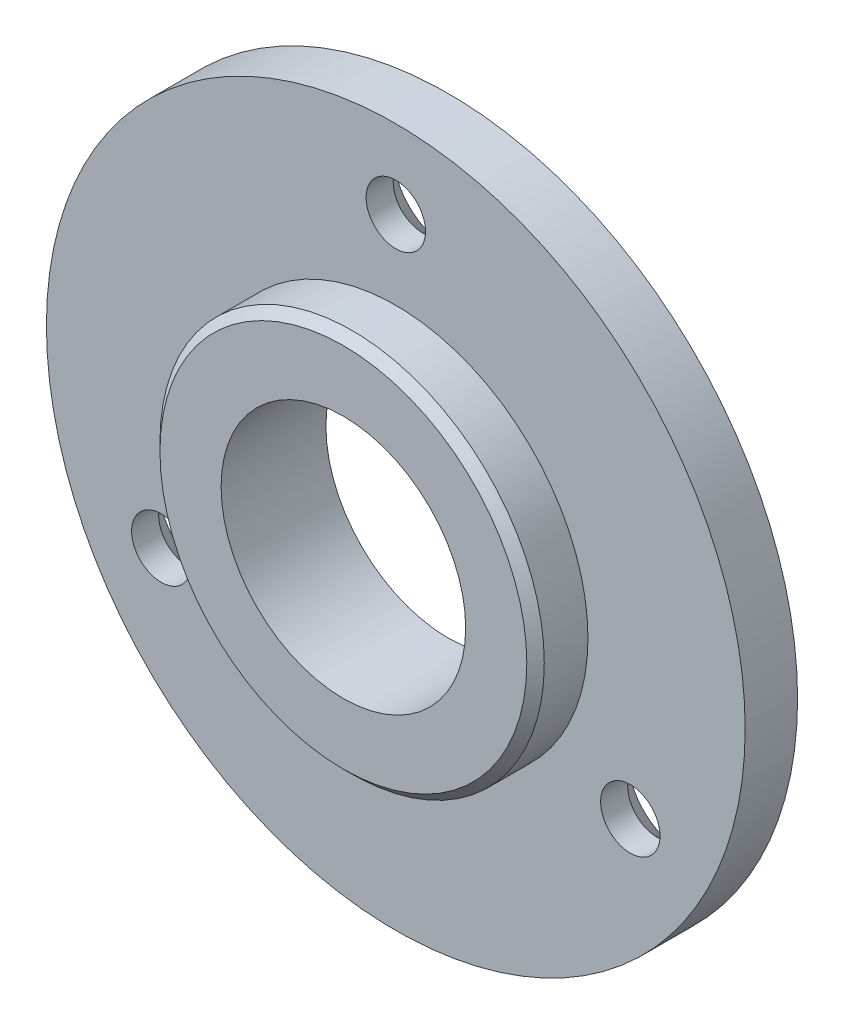
SolidWorks part; units mm, degrees
material "3.1325 (EN-AW 2017A)"
ref_plane "Plan de face" through (0, 0, 0) normal (0, 0, 1) x (1, 0, 0)
ref_plane "Plan de dessus" through (0, 0, 0) normal (0, 1, 0) x (1, 0, 0)
ref_plane "Plan de droite" through (0, 0, 0) normal (1, 0, 0) x (0, 0, -1)
sketch "Esquisse1" plane through (0, 0, 0) normal (0, 0, 1) x (1, 0, 0)
  circle A0 centre (0, 0) radius 20
extrude "Boss.-Extru.1" add sketch "Esquisse1" along normal blind 3
sketch "Esquisse2" plane through (0, 0, 3) normal (0, 0, 1) x (1, 0, 0)
  circle A0 centre (0, 0) radius 11
extrude "Boss.-Extru.2" add sketch "Esquisse2" along normal blind 3
chamfer "Chanfrein1" distance 0.5 angle 45 1 edges at (11, 0, 6)
sketch "Esquisse3" plane through (0, 0, 0) normal (0, 0, -1) x (-1, 0, 0)
  circle A0 centre (0, 0) radius 7
extrude "Enlèv. mat.-Extru.1" cut sketch "Esquisse3" against normal through all
hole_wizard "Fraisage pour vis à tête fraisée M32" positions "Esquisse12" profile "Esquisse11" countersink size "M3" standard "ISO" end condition through all
sketch "Esquisse12" plane through (0, 0, 0) normal (0, 0, -1) x (-1, 0, 0)
  point P0 (0, 15.5)
  dimension "D1" = 0
  dimension "D2" = 15.5
sketch "Esquisse11" plane through (0, 15.5, 0) normal (1, 0, 0) x (0, 1, 0)
  line L0 (0, 0) -> (0, 6)
  line L1 (0, 6) -> (1.7, 6)
  line L2 (1.7, 6) -> (1.7, 1.45)
  line L3 (1.7, 1.45) -> (3.15, 0)
  line L5 (3.15, 0) -> (0, 0)
  line L6 (-1.7, 1.45) -> (-3.15, 0) construction
  line L11 (0, -6.35) -> (0, 107.95) construction
  dimension "Diamètre du perçage jusqu'au prochain" = 3.4
  dimension "Profondeur du perçage jusqu'au prochain" = 6
  dimension "Diamètre du fraisage entrant" = 6.3
  dimension "Angle du fraisage entrant" = 90
pattern_circular "Répétition circulaire1" count 3 over 360 about axis through (0, 0, 0) along (0, 0, 1) of "Fraisage pour vis à tête fraisée M32"
